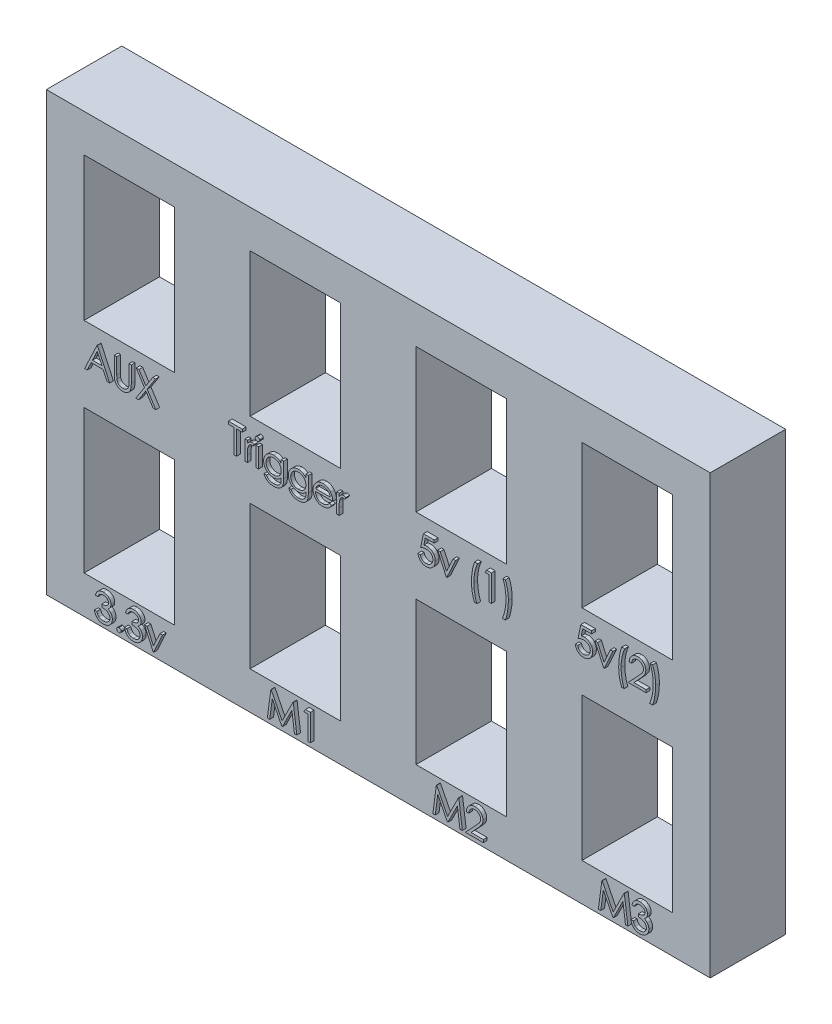
SolidWorks part; units mm, degrees
ref_plane "Front Plane" through (0, 0, 0) normal (0, 0, 1) x (1, 0, 0)
ref_plane "Top Plane" through (0, 0, 0) normal (0, 1, 0) x (1, 0, 0)
ref_plane "Right Plane" through (0, 0, 0) normal (1, 0, 0) x (0, 0, -1)
sketch "Sketch1" plane through (0, 0, 0) normal (0, 0, 1) x (1, 0, 0)
  line L1 (0, 0) -> (12, 0)
  line L2 (0, 0) -> (0, 19)
  line L3 (0, 19) -> (12, 19)
  line L4 (12, 0) -> (12, 19)
  line L5 (-5, -5) -> (17, -5)
  line L6 (-5, -5) -> (-5, 24)
  line L7 (-5, 24) -> (17, 24)
  line L8 (17, -5) -> (17, 24)
  dimension "D1" = 5
  dimension "D2" = 5
  dimension "D3" = 12
  dimension "D4" = 5
  dimension "D5" = 5
  dimension "D6" = 19
extrude "Boss-Extrude1" add sketch "Sketch1" along normal blind 10
pattern_linear "LPattern1" count 4 spacing 22 along (-1, 0, 0) count 2 spacing 29 along (0, 1, 0) of "Boss-Extrude1"
sketch "Sketch2" plane through (-71, 0, 0) normal (-1, 0, 0) x (0, 0, 1)
  line L0 (0, -5) -> (-20, -5)
  line L1 (-20, -5) -> (-20, 0)
  line L3 (0, 53) -> (0, -5) construction
  line L4 (-20, 0) -> (0, 0)
  dimension "D1" = 20
  dimension "D2" = 5
sketch "Sketch4" plane through (0, 0, 10) normal (0, 0, 1) x (1, 0, 0)
  line L0 (-71, 24) -> (17, 24) construction
  line L1 (-71, 53) -> (-71, -5) construction
  line L2 (17, -5) -> (17, 53) construction
  line L3 (-71, -4) -> (17, -4) construction
  line L4 (-71, -5) -> (17, -5) construction
  text T0 "    AUX       Trigger       5v (1)      5v(2)"
  text T1 "     3.3v          M1           M2           M3"
  dimension "D1" = 1
extrude "Boss-Extrude5" add sketch "Sketch4" along normal blind 0.5
